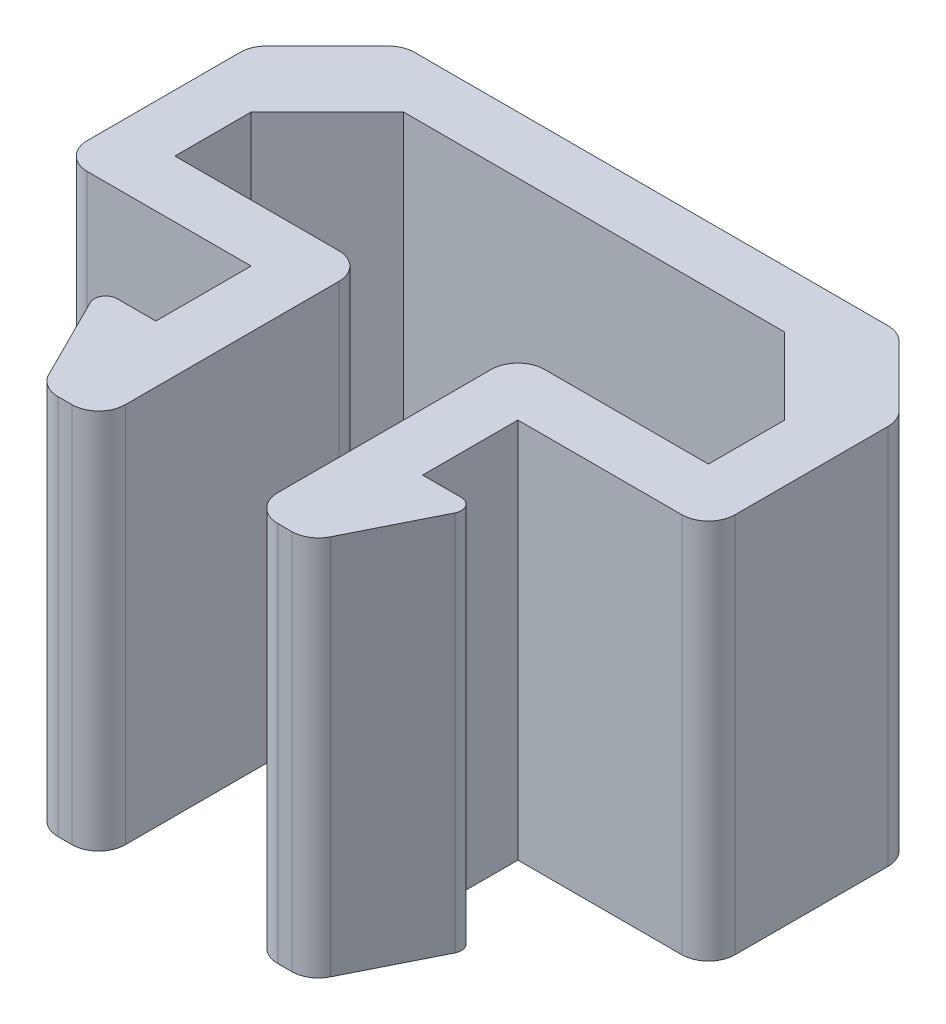
SolidWorks part; units mm, degrees
ref_plane "Front Plane" through (0, 0, 0) normal (0, 0, 1) x (1, 0, 0)
ref_plane "Top Plane" through (0, 0, 0) normal (0, 1, 0) x (1, 0, 0)
ref_plane "Right Plane" through (0, 0, 0) normal (1, 0, 0) x (0, 0, -1)
sketch "Sketch1" plane through (0, 0, 0) normal (0, 1, 0) x (1, 0, 0)
  line L0 (-1.7, -14.8452) -> (-1.7, -7.8452)
  line L1 (-3.2, -9.3452) -> (-3.2, -11.8452)
  line L2 (8.8, -2.3452) -> (-8.2, -2.3452)
  line L5 (-8.2, -2.3452) -> (-8.2, -9.3452)
  line L6 (-1.7, -14.8452) -> (-3.2, -14.8452)
  line L7 (-4.7, -11.8452) -> (-3.2, -14.8452)
  line L8 (7.3, -3.8452) -> (-6.7, -3.8452)
  line L10 (7.3, -7.8452) -> (2.3, -7.8452)
  line L11 (-6.7, -3.8452) -> (-6.7, -7.8452)
  line L16 (-1.7, -14.8452) -> (-3.2, -14.8452)
  line L18 (-3.2, -11.8452) -> (-4.7, -11.8452)
  line L21 (-3.2, -9.3452) -> (-8.2, -9.3452)
  line L22 (3.8, -9.3452) -> (8.8, -9.3452)
  line L23 (3.8, -11.8452) -> (5.3, -11.8452)
  line L24 (2.3, -14.8452) -> (3.8, -14.8452)
  line L25 (7.3, -3.8452) -> (7.3, -7.8452)
  line L26 (5.3, -11.8452) -> (3.8, -14.8452)
  line L27 (2.3, -14.8452) -> (3.8, -14.8452)
  line L28 (8.8, -2.3452) -> (8.8, -9.3452)
  line L29 (3.8, -9.3452) -> (3.8, -11.8452)
  line L30 (2.3, -14.8452) -> (2.3, -7.8452)
  line L31 (-1.7, -7.8452) -> (-6.7, -7.8452)
  dimension "D2" = 7
  dimension "D3" = 17
  dimension "D4" = 1.5
  dimension "D5" = 1.5
  dimension "D6" = 1.5
  dimension "D7" = 1.5
  dimension "D8" = 1.5
  dimension "D9" = 1.5
  dimension "D10" = 1.5
  dimension "D11" = 6.5
  dimension "D12" = 6.5
extrude "Boss-Extrude1" add sketch "Sketch1" along normal blind 10 contours L0 L31 L11 L8 L25 L10 L30 L24 L26 L23 L29 L22 L28 L2 L5 L21 L1 L18 L7 L6
chamfer "Chamfer1" distance 2 angle 45 4 edges at (-8.2, 5, 2.3452) (8.8, 5, 2.3452) (7.3, 5, 3.8452) (-6.7, 5, 3.8452)
fillet "Fillet1" radius 0.7 12 edges at (2.3, 5, 7.8452) (-1.7, 5, 7.8452) (-8.2, 5, 4.3452) (-6.2, 5, 2.3452) (6.8, 5, 2.3452) (8.8, 5, 4.3452) (3.8, 5, 14.8452) (2.3, 5, 14.8452) (-1.7, 5, 14.8452) (-3.2, 5, 14.8452) (8.8, 5, 9.3452) (-8.2, 5, 9.3452)
fillet "Fillet2" radius 0.3 2 edges at (5.3, 5, 11.8452) (-4.7, 5, 11.8452)
